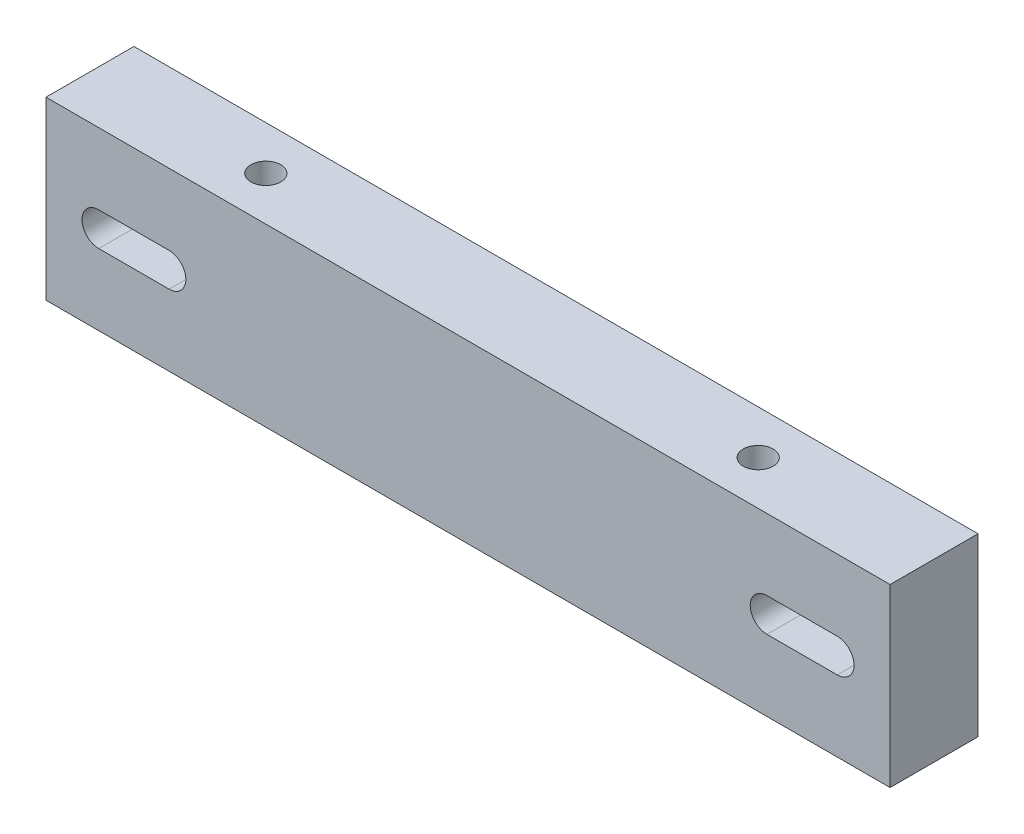
SolidWorks part; units mm, degrees
ref_plane "Alzado" through (0, 0, 0) normal (0, 0, 1) x (1, 0, 0)
ref_plane "Planta" through (0, 0, 0) normal (0, 1, 0) x (1, 0, 0)
ref_plane "Vista lateral" through (0, 0, 0) normal (1, 0, 0) x (0, 0, -1)
sketch "Croquis1" plane through (0, 0, 0) normal (0, 1, 0) x (1, 0, 0)
  line L1 (-120, 15) -> (120, 15)
  line L2 (-120, 15) -> (-120, -10)
  line L3 (-120, -10) -> (120, -10)
  line L4 (120, 15) -> (120, -10)
  dimension "D1" = 25
  dimension "D2" = 240
  dimension "D3" = 120
extrude "Saliente-Extruir1" add sketch "Croquis1" against normal blind 50
sketch "Croquis2" plane through (0, 0, 0) normal (0, 1, 0) x (1, 0, 0)
  line L0 (-120, 15) -> (-120, -10) construction
  line L1 (120, -10) -> (120, 15) construction
  line L2 (120, 15) -> (-120, 15) construction
  circle A0 centre (-70, 2.5) radius 4.25
  circle A1 centre (70, 2.5) radius 4.25
  dimension "D1" = 8.5
  dimension "D2" = 8.5
  dimension "D3" = 50
  dimension "D4" = 50
  dimension "D5" = 12.5
  dimension "D6" = 12.5
extrude "Cortar-Extruir1" cut sketch "Croquis2" against normal blind 25
sketch "Croquis3" plane through (0, 0, 10) normal (0, 0, 1) x (1, 0, 0)
  line L0 (-120, -50) -> (-120, 0) construction
  line L1 (-105, -20.2325) -> (-85, -20.2325)
  line L3 (-105, -29.7675) -> (-85, -29.7675)
  line L5 (85, -20.2325) -> (105, -20.2325)
  line L7 (85, -29.7675) -> (105, -29.7675)
  line L9 (120, -50) -> (120, 0) construction
  line L10 (-120, -50) -> (120, -50) construction
  arc A0 (-105, -20.2325) -> (-105, -29.7675) centre (-105, -25) ccw
  arc A1 (-85, -29.7675) -> (-85, -20.2325) centre (-85, -25) ccw
  arc A2 (85, -20.2325) -> (85, -29.7675) centre (85, -25) ccw
  arc A3 (105, -29.7675) -> (105, -20.2325) centre (105, -25) ccw
  point P18 (-120, -25)
  dimension "D1" = 20
  dimension "D2" = 20
  dimension "D3" = 15
  dimension "D4" = 15
  dimension "D5" = 25
  dimension "D6" = 25
extrude "Cortar-Extruir3" cut sketch "Croquis3" against normal through all
